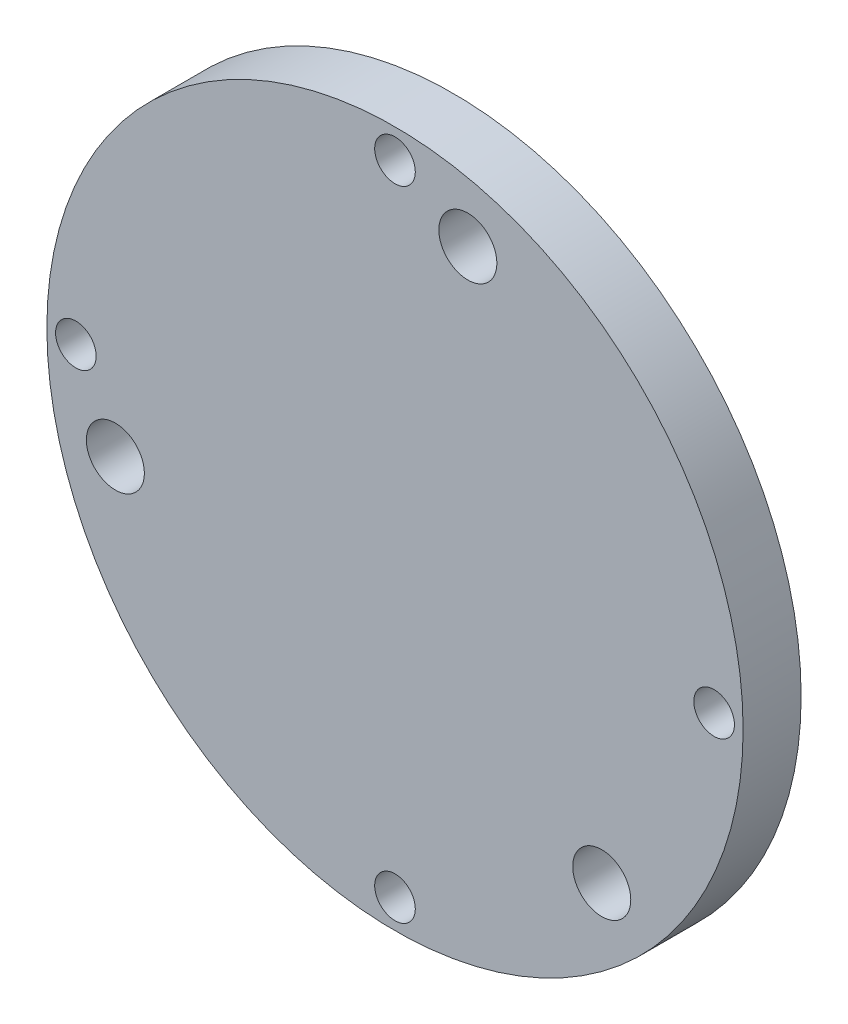
SolidWorks part; units mm, degrees
ref_plane "Front Plane" through (0, 0, 0) normal (0, 0, 1) x (1, 0, 0)
ref_plane "Top Plane" through (0, 0, 0) normal (0, 1, 0) x (1, 0, 0)
ref_plane "Right Plane" through (0, 0, 0) normal (1, 0, 0) x (0, 0, -1)
sketch "Sketch1" plane through (0, 0, 0) normal (0, 0, 1) x (1, 0, 0)
  circle A0 centre (0, 0) radius 30
  circle A1 centre (0, 0) radius 27.5 construction
  circle A2 centre (0, 27.5) radius 1.75
  circle A3 centre (27.5, 0) radius 1.75
  circle A4 centre (0, -27.5) radius 1.75
  circle A5 centre (-27.5, 0) radius 1.75
  circle A6 centre (0, 0) radius 25
  circle A8 centre (6.2786, 24.1987) radius 2.5
  circle A9 centre (17.8174, -17.5368) radius 2.5
  circle A10 centre (-24.096, -6.662) radius 2.5
  point P15 (0, 0)
  point P22 (0, 0)
extrude "Boss-Extrude1" add sketch "Sketch1" along normal blind 5 contours A10 A6 A9 A8 | A0 A10 A6 A8 A9 A5 A4 A3 A2
